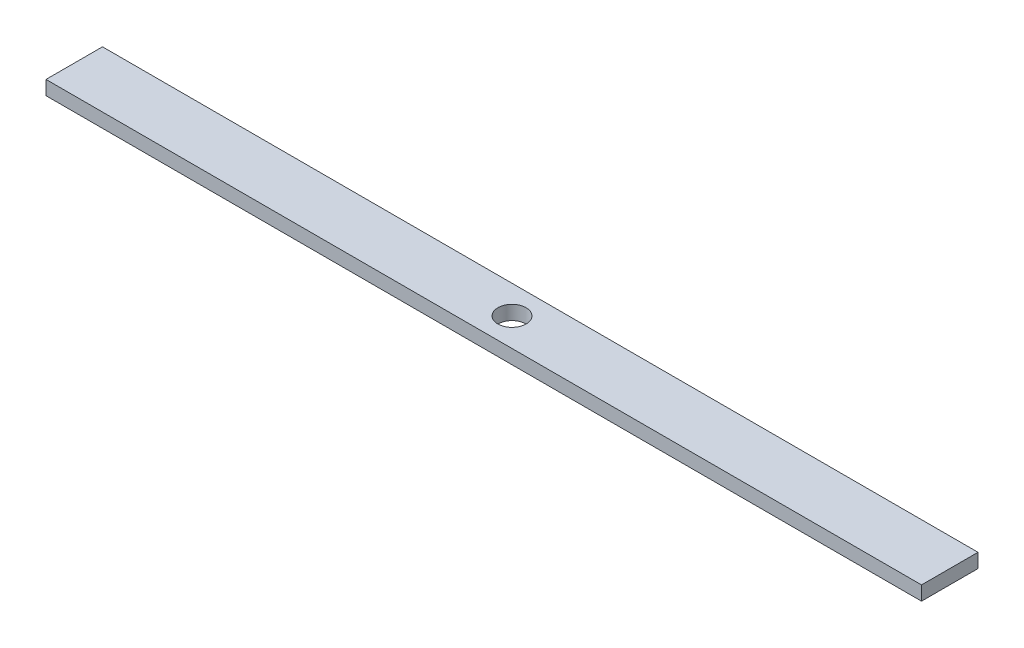
SolidWorks part; units mm, degrees
material "6061-T6 (SS)"
ref_plane "Front Plane" through (0, 0, 0) normal (0, 0, 1) x (1, 0, 0)
ref_plane "Top Plane" through (0, 0, 0) normal (0, 1, 0) x (1, 0, 0)
ref_plane "Right Plane" through (0, 0, 0) normal (1, 0, 0) x (0, 0, -1)
sketch "Sketch2" plane through (0, 0, 0) normal (0, 1, 0) x (1, 0, 0)
  line L1 (-196.85, 12.7) -> (196.85, 12.7)
  line L2 (-196.85, 12.7) -> (-196.85, -12.7)
  line L3 (-196.85, -12.7) -> (196.85, -12.7)
  line L4 (196.85, 12.7) -> (196.85, -12.7)
  line L5 (-196.85, 12.7) -> (196.85, -12.7) construction
  line L6 (-196.85, -12.7) -> (196.85, 12.7) construction
  circle A0 centre (0, 0) radius 6.35
  point P0 (0, 0)
  dimension "D1" = 25.4
  dimension "D2" = 393.7
extrude "Boss-Extrude1" add sketch "Sketch2" along normal blind 6.35
